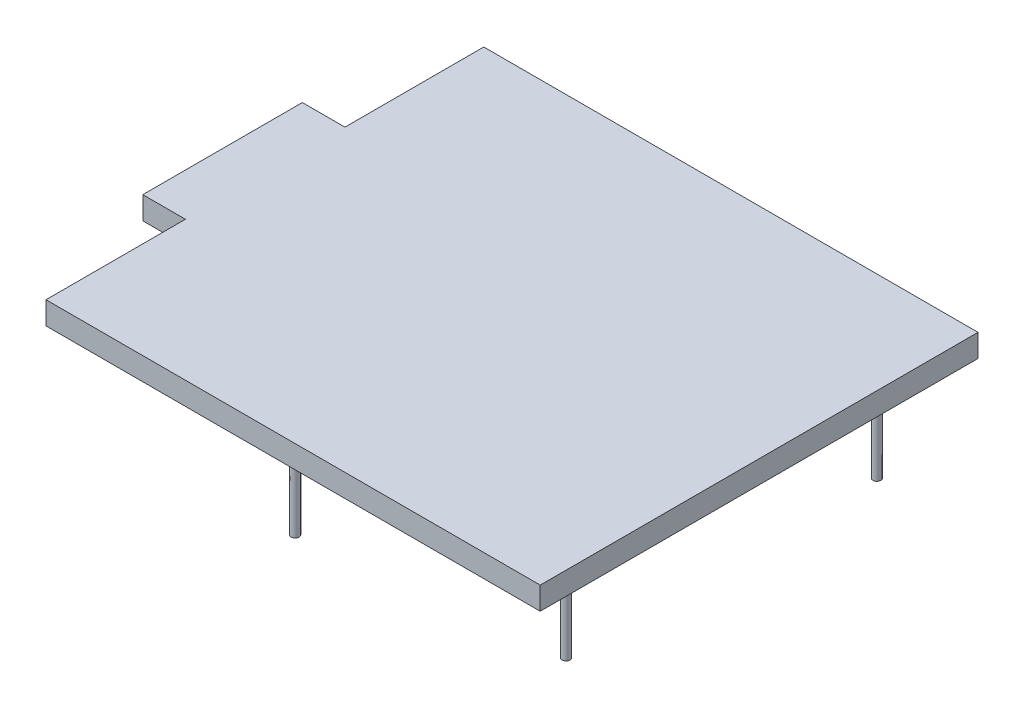
SolidWorks part; units mm, degrees
ref_plane "Front Plane" through (0, 0, 0) normal (0, 0, 1) x (1, 0, 0)
ref_plane "Top Plane" through (0, 0, 0) normal (0, 1, 0) x (1, 0, 0)
ref_plane "Right Plane" through (0, 0, 0) normal (1, 0, 0) x (0, 0, -1)
sketch "Sketch1" plane through (0, 0, 0) normal (0, 1, 0) x (1, 0, 0)
  line L0 (178.1945, -68.3693) -> (414.9225, -68.4963) construction
  line L1 (196.9905, 28.0237) -> (414.9225, 28.0237)
  line L2 (196.9905, 28.0237) -> (196.9905, -33.1903)
  line L3 (196.9905, -165.0163) -> (414.9225, -165.0163)
  line L4 (414.9225, 28.0237) -> (414.9225, -165.0163)
  line L5 (196.9905, 28.0237) -> (414.9225, -165.0163) construction
  line L6 (196.9905, -165.0163) -> (414.9225, 28.0237) construction
  line L7 (178.1945, -33.1903) -> (196.9905, -33.1903)
  line L8 (178.1945, -33.1903) -> (178.1945, -103.5483)
  line L9 (178.1945, -103.5483) -> (196.9905, -103.5483)
  line L10 (196.9905, -165.0163) -> (196.9905, -103.5483)
  dimension "D1" = 217.932
  dimension "D2" = 70.358
  dimension "D3" = 61.468
  dimension "D4" = 193.04
  dimension "D5" = 18.796
extrude "Boss-Extrude1" add sketch "Sketch1" along normal blind 10
sketch "Sketch2" plane through (0, 0, 0) normal (0, -1, 0) x (1, 0, 0)
  line L0 (178.1945, 68.6233) -> (414.9225, 68.4963) construction
  line L1 (196.9905, 165.0163) -> (414.9225, 165.0163) construction
  line L2 (196.9905, 165.0163) -> (196.9905, 103.8023) construction
  line L3 (196.9905, -28.0237) -> (414.9225, -28.0237) construction
  line L4 (414.9225, 165.0163) -> (414.9225, -28.0237) construction
  line L5 (196.9905, 165.0163) -> (414.9225, -28.0237) construction
  line L6 (196.9905, -28.0237) -> (414.9225, 165.0163) construction
  line L7 (178.1945, 103.8023) -> (196.9905, 103.8023) construction
  line L8 (178.1945, 103.8023) -> (178.1945, 33.4443) construction
  line L9 (178.1945, 33.4443) -> (196.9905, 33.4443) construction
  line L10 (196.9905, -28.0237) -> (196.9905, 33.4443) construction
  circle A0 centre (291.7005, 149.8425) radius 1.75
  circle A1 centre (398.3805, 137.0852) radius 1.75
  circle A2 centre (398.3069, -0.0747) radius 1.75
  circle A3 centre (291.6133, -12.7175) radius 1.75
  point P0 (305.9565, 68.4963)
  dimension "D6" = 3.5
  dimension "D1" = 217.932
  dimension "D2" = 70.358
  dimension "D3" = 61.468
  dimension "D4" = 193.04
  dimension "D5" = 18.796
  dimension "D7" = 81.28
  dimension "D8" = 68.58
  dimension "D9" = 94.71
  dimension "D10" = 106.68
extrude "Boss-Extrude2" add sketch "Sketch2" along normal blind 40
